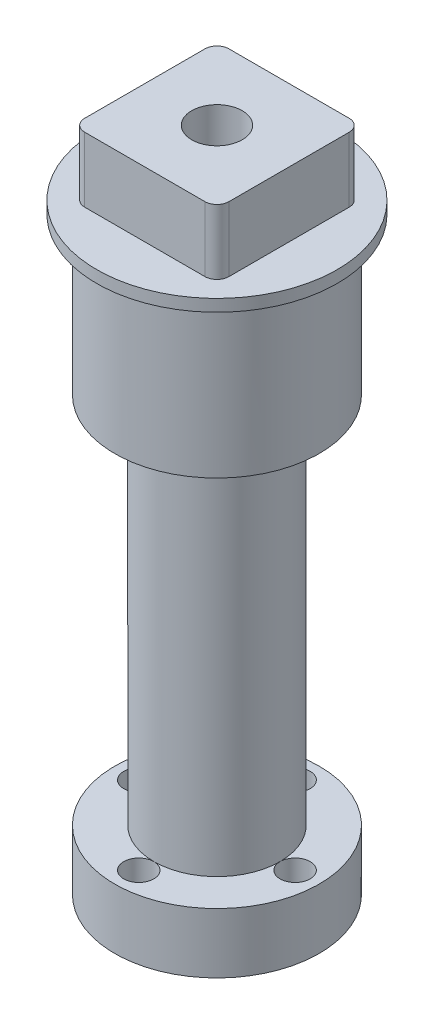
SolidWorks part; units mm, degrees
material "6061-T6 (SS)"
ref_plane "前视基准面" through (0, 0, 0) normal (0, 0, 1) x (1, 0, 0)
ref_plane "上视基准面" through (0, 0, 0) normal (0, 1, 0) x (1, 0, 0)
ref_plane "右视基准面" through (0, 0, 0) normal (1, 0, 0) x (0, 0, -1)
sketch "草图1" plane through (0, 0, 0) normal (0, 0, 1) x (1, 0, 0)
  line L0 (0, 0) -> (0, 22.2724) construction
  line L1 (-8.5, 36) -> (-5.25, 36)
  line L2 (-4.25, 0) -> (-8.5, 0)
  line L3 (-4.25, 0) -> (-4.25, 50)
  line L4 (-4.25, 50) -> (-8.5, 50)
  line L5 (-8.5, 0) -> (-8.5, 5)
  line L6 (-5.25, 36) -> (-5.25, 5)
  line L7 (-5.25, 5) -> (-8.5, 5)
  line L8 (-8.5, 36) -> (-8.5, 50)
  dimension "D1" = 8.5
  dimension "D2" = 17
  dimension "D3" = 50
  dimension "D4" = 36
  dimension "D5" = 5
  dimension "D6" = 1
revolve "旋转1" add sketch "草图1" angle 360 about L0
sketch "草图2" plane through (0, 50, 0) normal (0, 1, 0) x (1, 0, 0)
  circle A0 centre (0, 0) radius 6.5 construction
  circle A1 centre (0, 6.5) radius 1.25
  circle A2 centre (0, -6.5) radius 1.25
  circle A3 centre (-6.5, 0) radius 1.25
  circle A4 centre (6.5, 0) radius 1.25
  dimension "D1" = 13
  dimension "D2" = 2.5
extrude "切除-拉伸2" cut sketch "草图2" along normal blind 6 from surface at -50 starting at face at (0, 0, -4.25)
cosmetic thread "装饰螺纹线1" parameters "D2"=3
cosmetic thread "装饰螺纹线2" parameters "D2"=3
sketch "草图4" plane through (0, 50, 0) normal (0, 1, 0) x (1, 0, 0)
  line L1 (-6, 6) -> (6, 6)
  line L2 (-6, 6) -> (-6, -6)
  line L3 (-6, -6) -> (6, -6)
  line L4 (6, 6) -> (6, -6)
  line L5 (-6, 6) -> (6, -6) construction
  line L6 (-6, -6) -> (6, 6) construction
  point P0 (0, 0)
  dimension "D1" = 12
extrude "凸台-拉伸1" add sketch "草图4" along normal blind 5.4
fillet "圆角1" radius 1 4 edges at (6, 52.7, 6) (-6, 52.7, 6) (6, 52.7, -6) (-6, 52.7, -6)
sketch "草图5" plane through (0, 0, 0) normal (0, 0, 1) x (1, 0, 0)
  line L0 (0, 0) -> (0, 55.4) construction
  line L1 (-8.5, 50) -> (-10, 50)
  line L2 (-8.5, 50) -> (-8.5, 49)
  line L3 (-8.5, 49) -> (-10, 49)
  line L4 (-10, 50) -> (-10, 49)
  line L5 (5, 55.4) -> (-5, 55.4) construction
  dimension "D1" = 1.5
  dimension "D2" = 1
revolve "旋转2" add sketch "草图5" angle 360 about L0
sketch "草图6" plane through (0, 50, 0) normal (0, -1, 0) x (1, 0, 0)
  circle A1 centre (0, 0) radius 4.25
  circle A2 centre (0, 0) radius 4.25
  dimension "D1" = 0
extrude "凸台-拉伸2" add sketch "草图6" along normal blind 6
hole_wizard "M5 螺纹孔2" positions "草图10" profile "草图9" tap size "M5" standard "ISO" end condition through all
sketch "草图10" plane through (0, 55.4, 0) normal (0, 1, 0) x (1, 0, 0)
  point P0 (0, 0)
sketch "草图9" plane through (0, 55.4, 0) normal (1, 0, 0) x (0, 0, 1)
  line L0 (0, 0) -> (0, 55.4)
  line L1 (0, 55.4) -> (2.1, 55.4)
  line L2 (2.1, 55.4) -> (2.1, 0)
  line L5 (2.1, 0) -> (0, 0)
  line L11 (0, -6.35) -> (0, 107.95) construction
  dimension "通孔螺纹孔钻头直径" = 4.2
  dimension "通孔螺纹孔钻头深度" = 55.4
cosmetic thread "孔螺蚊线2" parameters "D2"=5
